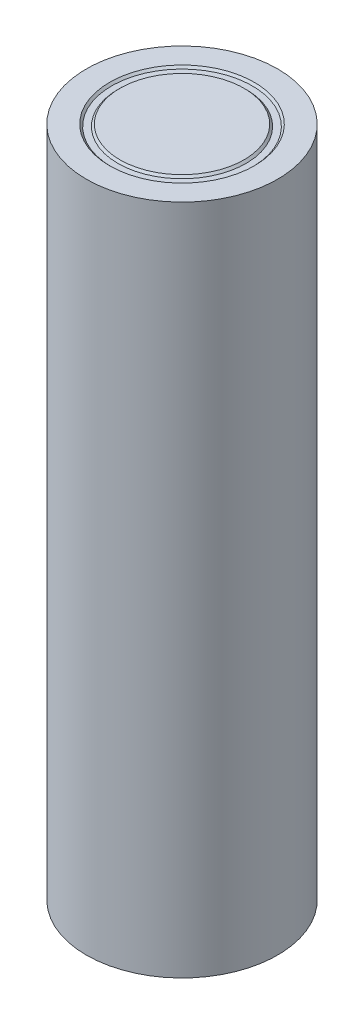
SolidWorks part; units mm, degrees
ref_plane "Front Plane" through (0, 0, 0) normal (0, 0, 1) x (1, 0, 0)
ref_plane "Top Plane" through (0, 0, 0) normal (0, 1, 0) x (1, 0, 0)
ref_plane "Right Plane" through (0, 0, 0) normal (1, 0, 0) x (0, 0, -1)
sketch "Sketch1" plane through (0, 0, 0) normal (0, 1, 0) x (1, 0, 0)
  circle A0 centre (0, 0) radius 9.25
  dimension "D1" = 18.5
extrude "Boss-Extrude1" add sketch "Sketch1" along normal blind 65
sketch "Sketch2" plane through (0, 65, 0) normal (0, 1, 0) x (1, 0, 0)
  circle A0 centre (0, 0) radius 7
  circle A1 centre (0, 0) radius 6
  dimension "D1" = 14
  dimension "D2" = 1
extrude "Cut-Extrude1" cut sketch "Sketch2" against normal blind 0.2 draft 45
